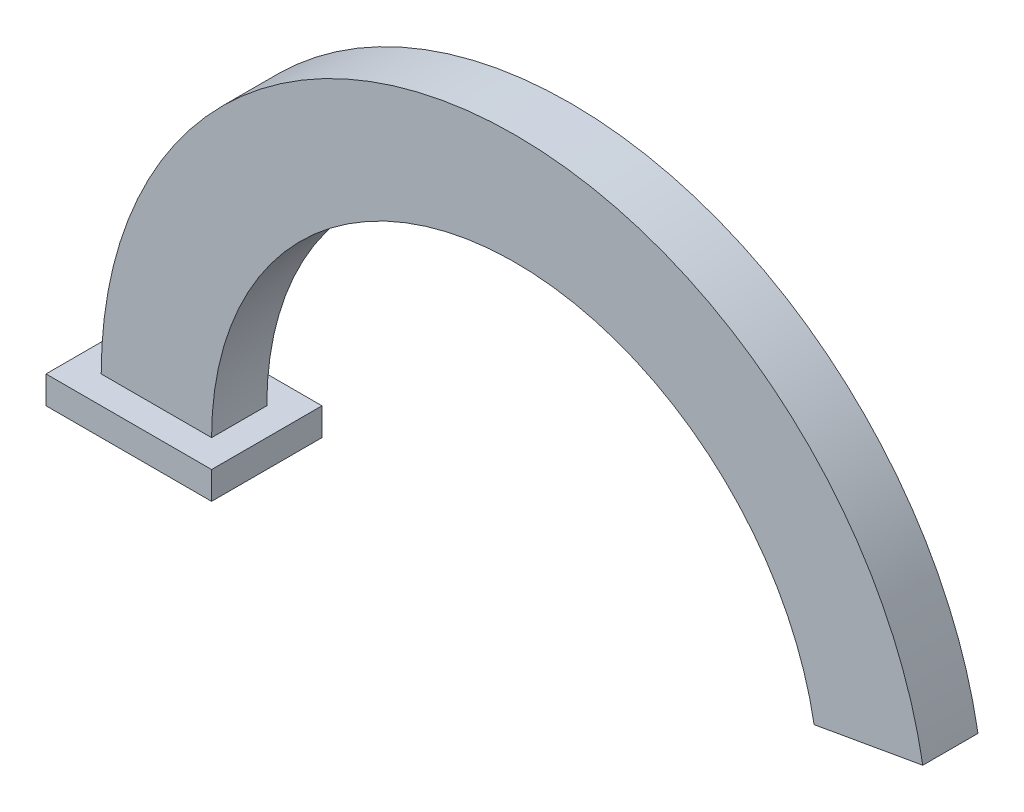
SolidWorks part; units mm, degrees
ref_plane "Front Plane" through (0, 0, 0) normal (0, 0, 1) x (1, 0, 0)
ref_plane "Top Plane" through (0, 0, 0) normal (0, 1, 0) x (1, 0, 0)
ref_plane "Right Plane" through (0, 0, 0) normal (1, 0, 0) x (0, 0, -1)
sketch "Sketch1" plane through (0, 0, 0) normal (0, 0, 1) x (1, 0, 0)
  line L0 (0, 0) -> (-75, 0)
  line L1 (0, 0) -> (73.8606, 13.0236)
  circle A0 centre (0, 0) radius 75
  circle A1 centre (0, 0) radius 55
  arc A2 (-75, 0) -> (73.8606, 13.0236) centre (0, 0) cw
extrude "Boss-Extrude1" add sketch "Sketch1" along normal blind 10 contours A1 L1 A0 L0
sketch "Sketch2" plane through (0, 0, 0) normal (0, -1, 0) x (1, 0, 0)
  line L0 (-75, 10) -> (-55, 0)
  line L1 (-55, 10) -> (-75, 0)
  line L3 (-80, 15) -> (-50, 15)
  line L4 (-80, 15) -> (-80, -5)
  line L5 (-80, -5) -> (-50, -5)
  line L6 (-50, 15) -> (-50, -5)
  line L7 (-80, 15) -> (-50, -5) construction
  line L8 (-80, -5) -> (-50, 15) construction
  point P8 (-65, 5)
  line M3 (-75, 0) -> (-55, 0)
  line M4 (-55, 0) -> (-55, 10)
  line M5 (-55, 10) -> (-75, 10)
  line M6 (-75, 10) -> (-75, 0)
  dimension "D1" = 30
  dimension "D2" = 20
extrude "Boss-Extrude2" add sketch "Sketch2" along normal blind 5 contours L6 L3 L4 L5 M3 M6 M5 M4 | L1 L0 M6 | L1 L0 M5 | L1 L0 M4 | L0 L1 M3
